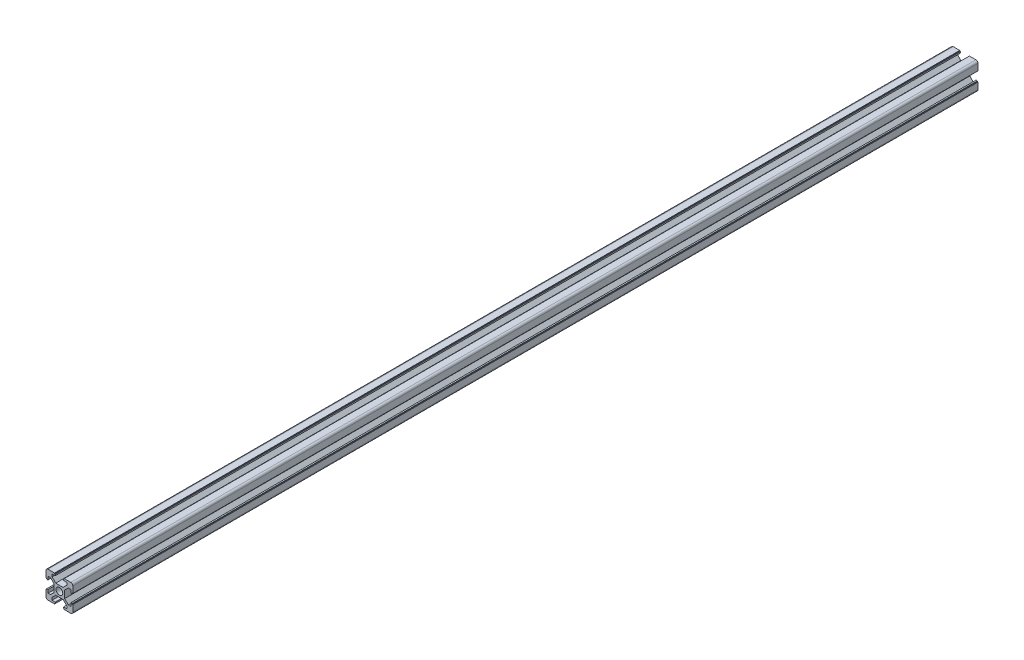
SolidWorks part; units mm, degrees
ref_plane "前视基准面" through (0, 0, 0) normal (0, 0, 1) x (1, 0, 0)
ref_plane "上视基准面" through (0, 0, 0) normal (0, 1, 0) x (1, 0, 0)
ref_plane "右视基准面" through (0, 0, 0) normal (1, 0, 0) x (0, 0, -1)
sketch "草图1" plane through (0, 0, 0) normal (0, 0, 1) x (1, 0, 0)
  line L0 (-3.6, 10) -> (-3.6, 9.5)
  line L1 (-3.6, 9.5) -> (-3.1, 9.5)
  line L2 (-3.1, 9.5) -> (-3.1, 8.5)
  line L3 (-3.1, 8.5) -> (-5.5, 8.5)
  line L4 (-8.5, -10) -> (-3.6, -10)
  line L5 (-10, -8.5) -> (-10, -3.6)
  line L6 (8.5, 10) -> (3.6, 10)
  line L7 (10, 8.5) -> (10, 3.6)
  line L8 (0, 14.8756) -> (0, 0) construction
  line L9 (0, 0) -> (14.1675, 0) construction
  line L10 (-5.5, 8.5) -> (-5.5, 6.65)
  line L11 (-5.5, 6.65) -> (-2.75, 3.9)
  line L12 (-2.75, 3.9) -> (2.75, 3.9)
  line L13 (5.5, 6.65) -> (2.75, 3.9)
  line L14 (5.5, 8.5) -> (5.5, 6.65)
  line L15 (3.1, 8.5) -> (5.5, 8.5)
  line L16 (3.1, 9.5) -> (3.1, 8.5)
  line L17 (3.6, 9.5) -> (3.1, 9.5)
  line L18 (3.6, 10) -> (3.6, 9.5)
  line L19 (-3.6, 10) -> (-8.5, 10)
  line L20 (10, 3.6) -> (9.5, 3.6)
  line L21 (9.5, 3.6) -> (9.5, 3.1)
  line L22 (9.5, 3.1) -> (8.5, 3.1)
  line L23 (8.5, 3.1) -> (8.5, 5.5)
  line L24 (8.5, 5.5) -> (6.65, 5.5)
  line L25 (6.65, 5.5) -> (3.9, 2.75)
  line L26 (3.9, 2.75) -> (3.9, -2.75)
  line L27 (6.65, -5.5) -> (3.9, -2.75)
  line L28 (8.5, -5.5) -> (6.65, -5.5)
  line L29 (8.5, -3.1) -> (8.5, -5.5)
  line L30 (9.5, -3.1) -> (8.5, -3.1)
  line L31 (9.5, -3.6) -> (9.5, -3.1)
  line L32 (10, -3.6) -> (9.5, -3.6)
  line L33 (3.6, -10) -> (3.6, -9.5)
  line L34 (3.6, -9.5) -> (3.1, -9.5)
  line L35 (3.1, -9.5) -> (3.1, -8.5)
  line L36 (3.1, -8.5) -> (5.5, -8.5)
  line L37 (5.5, -8.5) -> (5.5, -6.65)
  line L38 (5.5, -6.65) -> (2.75, -3.9)
  line L39 (2.75, -3.9) -> (-2.75, -3.9)
  line L40 (-5.5, -6.65) -> (-2.75, -3.9)
  line L41 (-5.5, -8.5) -> (-5.5, -6.65)
  line L42 (-3.1, -8.5) -> (-5.5, -8.5)
  line L43 (-3.1, -9.5) -> (-3.1, -8.5)
  line L44 (-3.6, -9.5) -> (-3.1, -9.5)
  line L45 (-3.6, -10) -> (-3.6, -9.5)
  line L46 (-10, -3.6) -> (-9.5, -3.6)
  line L47 (-9.5, -3.6) -> (-9.5, -3.1)
  line L48 (-9.5, -3.1) -> (-8.5, -3.1)
  line L49 (-8.5, -3.1) -> (-8.5, -5.5)
  line L50 (-8.5, -5.5) -> (-6.65, -5.5)
  line L51 (-6.65, -5.5) -> (-3.9, -2.75)
  line L52 (-3.9, -2.75) -> (-3.9, 2.75)
  line L53 (-6.65, 5.5) -> (-3.9, 2.75)
  line L54 (-8.5, 5.5) -> (-6.65, 5.5)
  line L55 (-8.5, 3.1) -> (-8.5, 5.5)
  line L56 (-9.5, 3.1) -> (-8.5, 3.1)
  line L57 (-9.5, 3.6) -> (-9.5, 3.1)
  line L58 (-10, 3.6) -> (-9.5, 3.6)
  line L59 (3.6, -10) -> (8.5, -10)
  line L60 (-10, 3.6) -> (-10, 8.5)
  line L61 (10, -3.6) -> (10, -8.5)
  circle A0 centre (0, 0) radius 2.5
  arc A1 (-10, 8.5) -> (-8.5, 10) centre (-8.5, 8.5) cw
  arc A2 (10, 8.5) -> (8.5, 10) centre (8.5, 8.5) ccw
  arc A3 (-8.5, -10) -> (-10, -8.5) centre (-8.5, -8.5) cw
  arc A4 (8.5, -10) -> (10, -8.5) centre (8.5, -8.5) ccw
  point P0 (-10, 0)
  point P1 (10, 0)
  point P2 (0, 10)
  point P3 (0, -10)
  point P4 (0, 0)
  point P5 (-10, -10)
  point P6 (10, -10)
  point P7 (10, 10)
  point P8 (-10, 10)
  point P13 (0, 0)
  dimension "D1" = 11
  dimension "D2" = 20
  dimension "D3" = 6.2
  dimension "D4" = 7.2
  dimension "D5" = 6.1
  dimension "D6" = 5
  dimension "D7" = 1.5
  dimension "D8" = 45
  dimension "D9" = 0.5
  dimension "D10" = 1
  dimension "D11" = 5.5
extrude "凸台-拉伸1" add sketch "草图1" along normal blind 700
sketch "草图2" plane through (-10, 0, 0) normal (-1, 0, 0) x (0, 0, 1)
  line L6 (700, -11.8187) -> (683.4723, -11.8187)
  line L7 (683.4723, -11.8187) -> (683.4723, 10.6791)
  line L8 (683.4723, 10.6791) -> (700, 10.6791)
  line L9 (700, 10.6791) -> (700, -11.8187)
extrude "切除-拉伸1" cut sketch "草图2" against normal through all
sketch "草图3" plane through (-10, 0, 0) normal (-1, 0, 0) x (0, 0, 1)
  line L1 (0, -11.0028) -> (8.365, -11.0028)
  line L2 (8.365, -11.0028) -> (8.365, 11.9972)
  line L3 (8.365, 11.9972) -> (0, 11.9972)
  line L4 (0, 11.9972) -> (0, -11.0028)
extrude "切除-拉伸2" cut sketch "草图3" against normal through all
